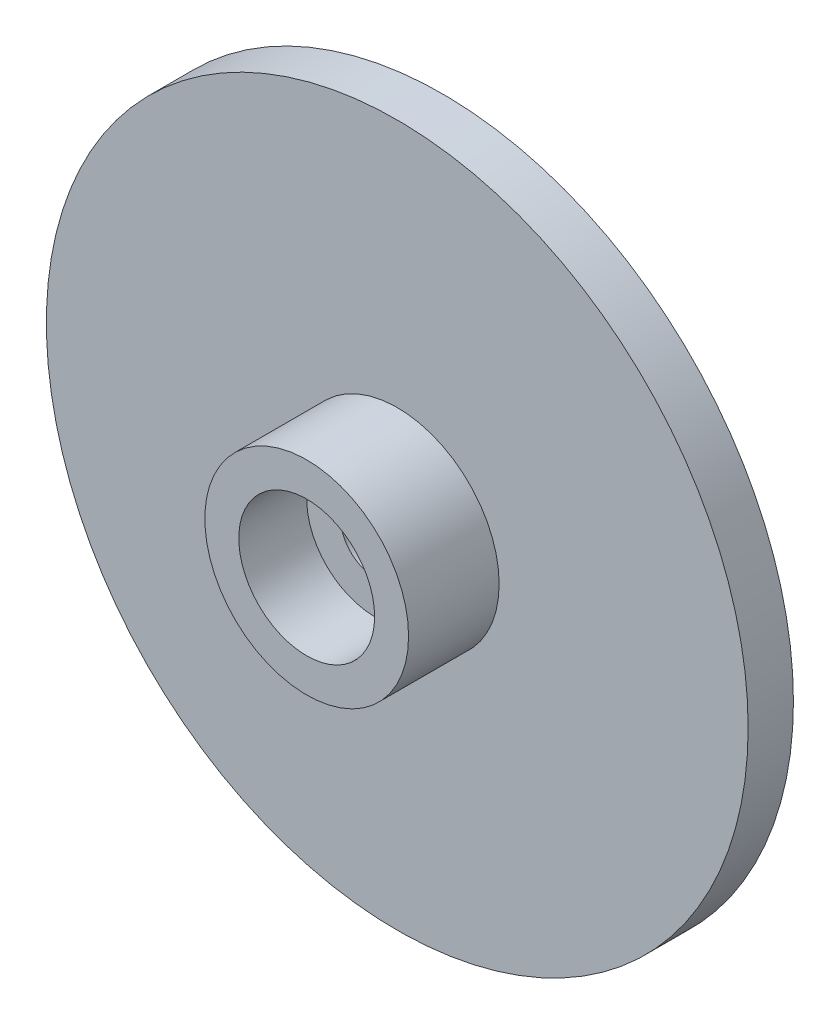
SolidWorks part; units mm, degrees
ref_plane "Piano frontale" through (0, 0, 0) normal (0, 0, 1) x (1, 0, 0)
ref_plane "Piano superiore" through (0, 0, 0) normal (0, 1, 0) x (1, 0, 0)
ref_plane "Piano destro" through (0, 0, 0) normal (1, 0, 0) x (0, 0, -1)
sketch "Schizzo1" plane through (0, 0, 0) normal (0, 0, 1) x (1, 0, 0)
  circle A0 centre (0, 0) radius 15.5
  dimension "D1" = 31
extrude "Estrusione-Estrusione1" add sketch "Schizzo1" along normal blind 2
sketch "Schizzo2" plane through (0, 0, 2) normal (0, 0, 1) x (1, 0, 0)
  circle A0 centre (0, 0) radius 4.5
  circle A1 centre (0, 0) radius 3
  dimension "D1" = 6
  dimension "D2" = 9
extrude "Estrusione-Estrusione2" add sketch "Schizzo2" along normal blind 4
sketch "Schizzo3" plane through (0, 0, 2) normal (0, 0, 1) x (1, 0, 0)
  circle A0 centre (0, 0) radius 3
extrude "Estrusione-Estrusione3" add sketch "Schizzo3" along normal blind 1
sketch "Schizzo4" plane through (0, 0, 0) normal (0, 0, -1) x (-1, 0, 0)
  circle A0 centre (0, 0) radius 4.5
  circle A1 centre (0, 0) radius 3.5
  circle A2 centre (0, 0) radius 3
  dimension "D1" = 9
  dimension "D2" = 6
  dimension "D3" = 7
extrude "Taglio-Estrusione1" cut sketch "Schizzo4" against normal blind 1 contours A2 | A0 A1
sketch "Schizzo5" plane through (0, 0, 1) normal (0, 0, -1) x (-1, 0, 0)
  circle A0 centre (0, 0) radius 1.5
extrude "Taglio-Estrusione2" cut sketch "Schizzo5" against normal blind 12
